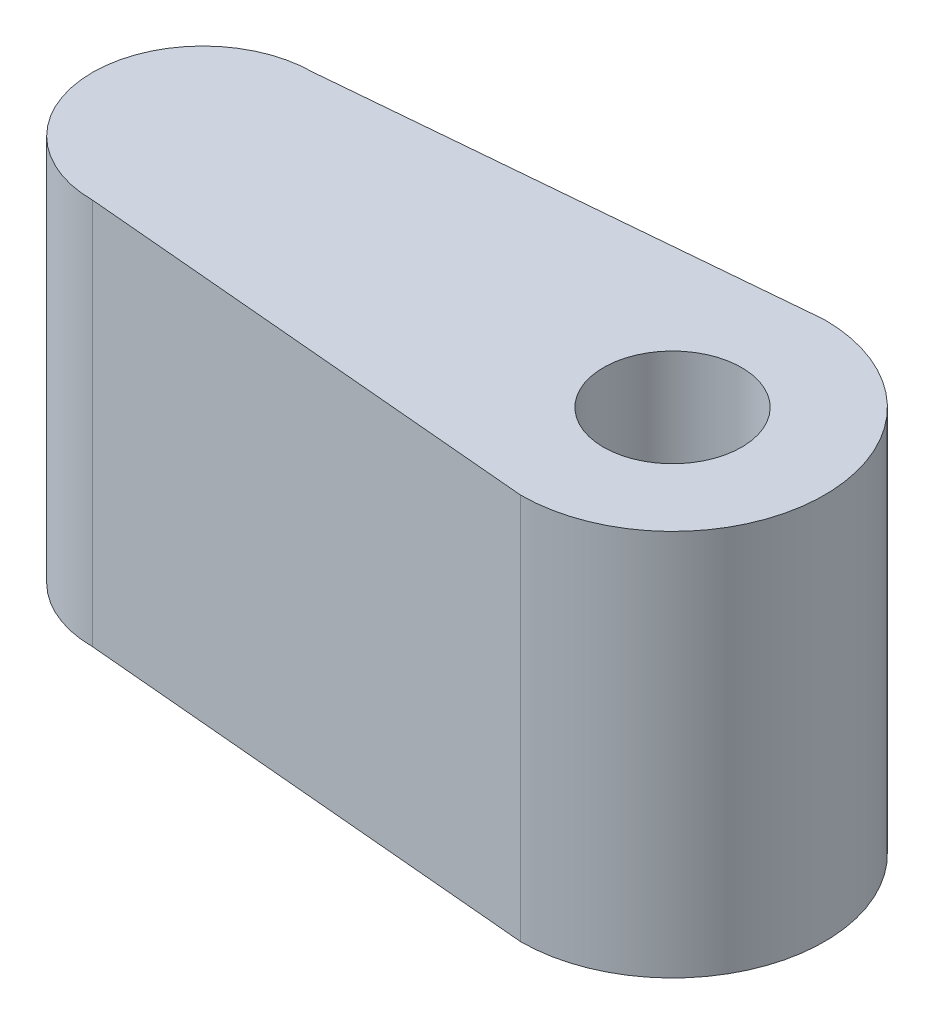
SolidWorks part; units mm, degrees
ref_plane "Front Plane" through (0, 0, 0) normal (0, 0, 1) x (1, 0, 0)
ref_plane "Top Plane" through (0, 0, 0) normal (0, 1, 0) x (1, 0, 0)
ref_plane "Right Plane" through (0, 0, 0) normal (1, 0, 0) x (0, 0, -1)
sketch "Sketch1" plane through (0, 0, 0) normal (0, 1, 0) x (1, 0, 0)
  line L0 (0, 0) -> (-8.5, 0) construction
  line L1 (-8.5, 2) -> (0, 2.75)
  line L2 (-8.5, -2) -> (0, -2.75)
  circle A0 centre (0, 0) radius 1.25
  arc A1 (-0.4815, -2.7075) -> (-0.4815, 2.7075) centre (0, 0) ccw
  arc A2 (-8.5, 2) -> (-8.5, -2) centre (-8.5, 0) ccw
  dimension "D1" = 2.5
  dimension "D2" = 5.5
  dimension "D3" = 4
  dimension "D4" = 8.5
extrude "Boss-Extrude1" add sketch "Sketch1" along normal blind 7
ref_plane "Plane1" through (-10.5, 0, 0) normal (-1, 0, 0) x (0, 0, 1)
sketch "Sketch2" plane through (-10.5, 0, 0) normal (-1, 0, 0) x (0, 0, 1)
  line L0 (0, 0) -> (0, 7) construction
  line L1 (2, 7) -> (-2, 7) construction
  line L2 (2, 7) -> (-2, 7) construction
  line L3 (-2, 0) -> (2, 0) construction
  line L4 (-2, 0) -> (2, 0) construction
  circle A0 centre (0, 3.5) radius 1.2
  dimension "D1" = 2.4
extrude "Cut-Extrude1" cut sketch "Sketch2" against normal blind 8
ref_plane "Plane2" through (0, 3.5, 0) normal (0, -1, 0) x (-1, 0, 0)
